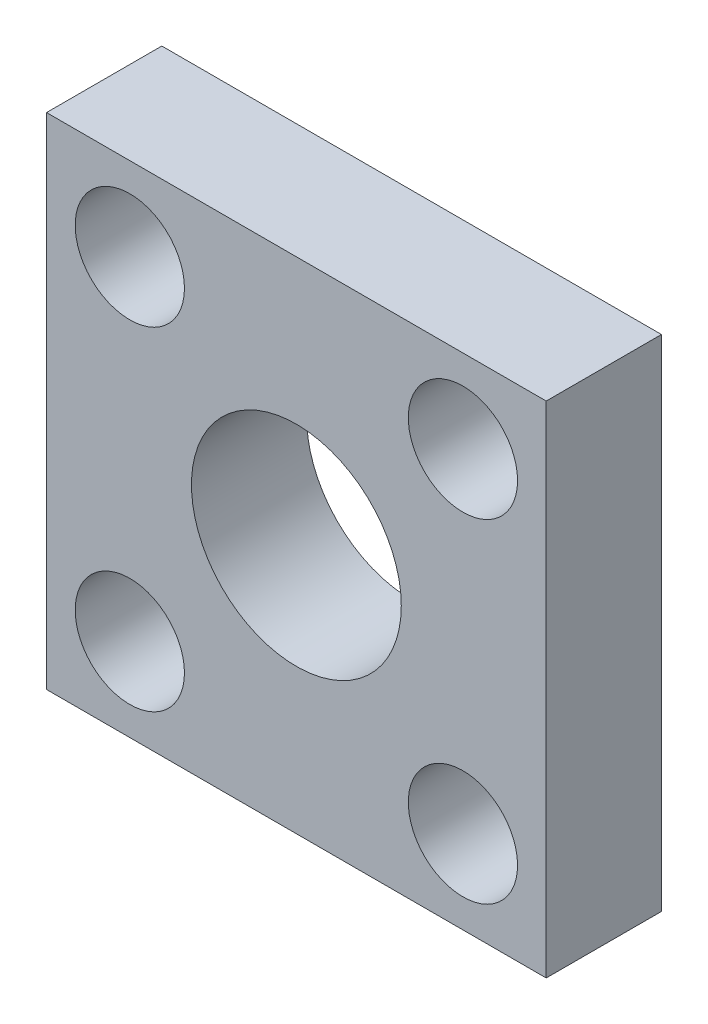
SolidWorks part; units mm, degrees
ref_plane "Front Plane" through (0, 0, 0) normal (0, 0, 1) x (1, 0, 0)
ref_plane "Top Plane" through (0, 0, 0) normal (0, 1, 0) x (1, 0, 0)
ref_plane "Right Plane" through (0, 0, 0) normal (1, 0, 0) x (0, 0, -1)
sketch "Sketch1" plane through (0, 0, 0) normal (0, 0, 1) x (1, 0, 0)
  line L0 (9.525, 19.05) -> (9.525, 0) construction
  line L1 (0, 0) -> (19.05, 0)
  line L2 (0, 0) -> (0, 19.05)
  line L3 (0, 19.05) -> (19.05, 19.05)
  line L4 (19.05, 0) -> (19.05, 19.05)
  line L5 (0, 9.525) -> (19.05, 9.525) construction
  circle A0 centre (3.175, 3.175) radius 2.0828
  circle A1 centre (3.175, 15.875) radius 2.0828
  circle A2 centre (15.875, 15.875) radius 2.0828
  circle A3 centre (15.875, 3.175) radius 2.0828
  circle A4 centre (9.525, 9.525) radius 4
  dimension "D1" = 4.1656
  dimension "D8" = 8
  dimension "D2" = 12.7
  dimension "D3" = 12.7
  dimension "D4" = 19.05
  dimension "D5" = 19.05
  dimension "D6" = 12.7
  dimension "D7" = 12.7
extrude "Boss-Extrude1" add sketch "Sketch1" along normal blind 4.3942
